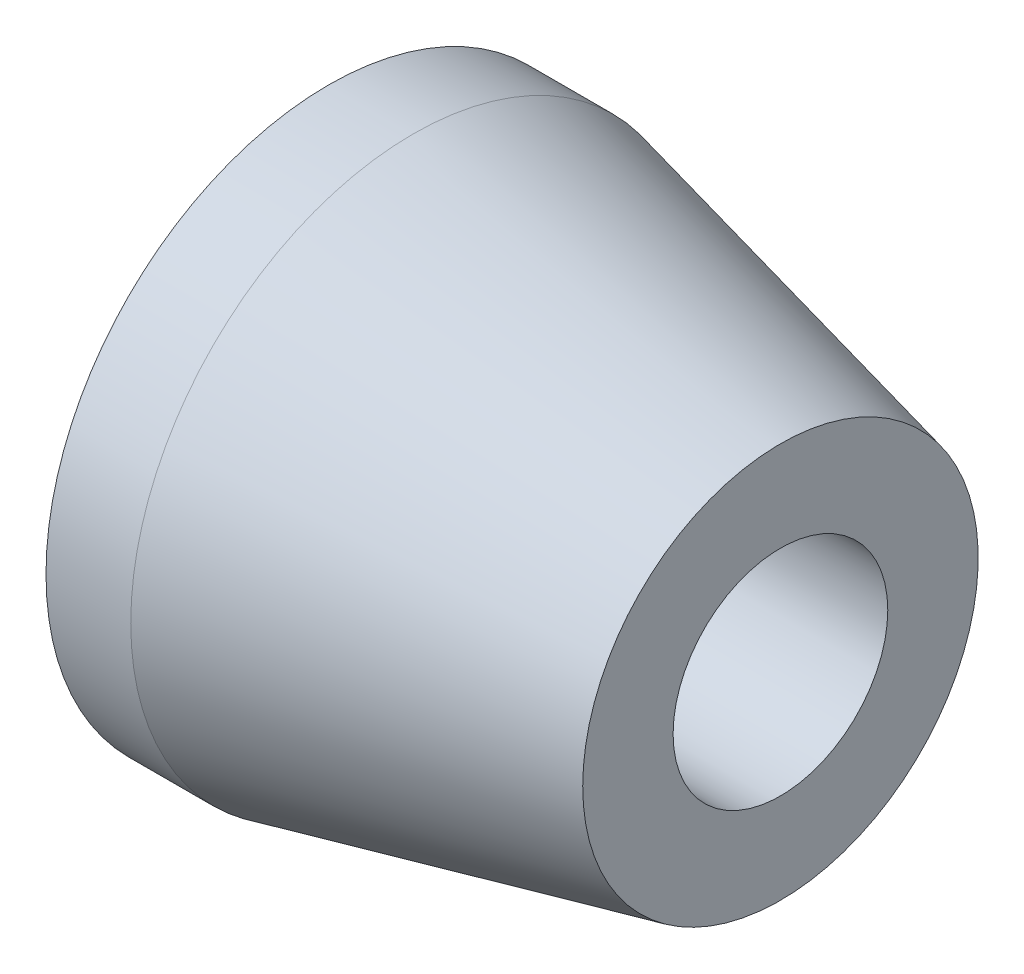
SolidWorks part; units mm, degrees
material "1023 Carbon Steel Sheet (SS)"
ref_plane "Front Plane" through (0, 0, 0) normal (0, 0, 1) x (1, 0, 0)
ref_plane "Top Plane" through (0, 0, 0) normal (0, 1, 0) x (1, 0, 0)
ref_plane "Right Plane" through (0, 0, 0) normal (1, 0, 0) x (0, 0, -1)
sketch "Sketch1" plane through (0, 0, 0) normal (1, 0, 0) x (0, 0, -1)
  circle A0 centre (0, 0) radius 10
  dimension "D1" = 20
extrude "Boss-Extrude1" add sketch "Sketch1" along normal blind 3
sketch "Sketch2" plane through (0, 0, 0) normal (-1, 0, 0) x (0, 0, 1)
  circle A0 centre (0, 0) radius 5.5
  dimension "D1" = 11
extrude "Cut-Extrude1" cut sketch "Sketch2" against normal blind 2
ref_plane "Plane1" through (16, 0, 0) normal (-1, 0, 0) x (0, 0, 1)
sketch "Sketch3" plane through (16, 0, 0) normal (-1, 0, 0) x (0, 0, 1)
  circle A0 centre (0, 0) radius 7
loft "Loft1" add profiles "Sketch3" section "Sketch3" section edge at (3, 0, -10)
sketch "Sketch4" plane through (16, 0, 0) normal (1, 0, 0) x (0, 0, -1)
  circle A0 centre (0, 0) radius 3.8
  dimension "D1" = 7.6
extrude "Cut-Extrude2" cut sketch "Sketch4" against normal up to surface (14 mm away) up to face at (2, 0, 5.5)
